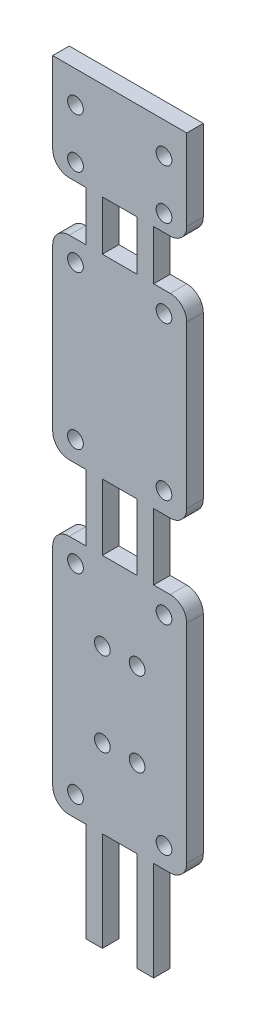
SolidWorks part; units mm, degrees
ref_plane "Front Plane" through (0, 0, 0) normal (0, 0, 1) x (1, 0, 0)
ref_plane "Top Plane" through (0, 0, 0) normal (0, 1, 0) x (1, 0, 0)
ref_plane "Right Plane" through (0, 0, 0) normal (1, 0, 0) x (0, 0, -1)
sketch "Sketch1" plane through (0, 0, 0) normal (0, 0, 1) x (1, 0, 0)
  line L0 (4, 26) -> (2, 26)
  line L1 (0, 1.5) -> (16.2, 1.5) construction
  line L2 (0, 14) -> (4, 14) construction
  line L3 (0, 14) -> (0, 1.5) construction
  line L4 (6, 14) -> (6, 26)
  line L5 (4, 14) -> (4, 26)
  line L6 (0, 28) -> (0, 53.14)
  line L7 (0, 94.665) -> (0, 104.46)
  line L8 (6, 14) -> (10.2, 14) construction
  line L9 (8.1, 1.5) -> (8.1, 104.46) construction
  line L10 (0, 104.46) -> (16.2, 104.46)
  line L11 (6, 63.14) -> (10.2, 63.14)
  line L12 (6, 55.14) -> (10.2, 55.14)
  line L13 (6, 92.665) -> (10.2, 92.665)
  line L14 (6, 86.665) -> (10.2, 86.665)
  line L15 (16.2, 84.665) -> (16.2, 65.14)
  line L16 (10.2, 86.665) -> (10.2, 92.665)
  line L17 (14.2, 55.14) -> (12.2, 55.14)
  line L18 (2, 92.665) -> (4, 92.665)
  line L19 (2, 86.665) -> (4, 86.665)
  line L20 (2, 63.14) -> (4, 63.14)
  line L21 (10.2, 55.14) -> (10.2, 63.14)
  line L22 (4, 86.665) -> (4, 92.665)
  line L23 (4, 55.14) -> (4, 63.14)
  line L24 (6, 55.14) -> (6, 63.14)
  line L25 (2, 55.14) -> (4, 55.14)
  line L26 (6, 86.665) -> (6, 92.665)
  line L27 (12.2, 55.14) -> (12.2, 63.14)
  line L28 (12.2, 86.665) -> (12.2, 92.665)
  line L29 (14.2, 63.14) -> (12.2, 63.14)
  line L30 (14.2, 86.665) -> (12.2, 86.665)
  line L31 (14.2, 92.665) -> (12.2, 92.665)
  line L32 (6, 26) -> (10.2, 26)
  line L33 (4, 14) -> (6, 14)
  line L34 (16.2, 94.665) -> (16.2, 104.46)
  line L35 (16.2, 28) -> (16.2, 53.14)
  line L36 (12.2, 14) -> (12.2, 26)
  line L37 (10.2, 14) -> (10.2, 26)
  line L38 (16.2, 14) -> (16.2, 1.5) construction
  line L39 (16.2, 14) -> (12.2, 14) construction
  line L40 (12.2, 26) -> (14.2, 26)
  line L41 (10.2, 14) -> (12.2, 14)
  line L58 (0, 84.665) -> (0, 65.14)
  circle A0 centre (2.85, 11.5) radius 0.95 construction
  circle A1 centre (13.45, 94.665) radius 0.95
  circle A2 centre (13.45, 84.165) radius 0.95
  circle A3 centre (2.85, 5.5) radius 0.95 construction
  circle A4 centre (13.45, 65.64) radius 0.95
  circle A5 centre (13.45, 52.64) radius 0.95
  circle A6 centre (13.45, 28.5) radius 0.95
  circle A7 centre (10.2, 35.5) radius 0.95
  arc A8 (16.2, 28) -> (14.2, 26) centre (14.2, 28) cw
  circle A9 centre (10.2, 45.64) radius 0.95
  arc A10 (2, 86.665) -> (0, 84.665) centre (2, 84.665) ccw
  arc A11 (14.2, 55.14) -> (16.2, 53.14) centre (14.2, 53.14) cw
  circle A12 centre (13.45, 100.665) radius 0.95
  arc A13 (16.2, 94.665) -> (14.2, 92.665) centre (14.2, 94.665) cw
  arc A14 (16.2, 65.14) -> (14.2, 63.14) centre (14.2, 65.14) cw
  arc A15 (0, 65.14) -> (2, 63.14) centre (2, 65.14) ccw
  arc A16 (0, 94.665) -> (2, 92.665) centre (2, 94.665) ccw
  arc A17 (14.2, 86.665) -> (16.2, 84.665) centre (14.2, 84.665) cw
  circle A18 centre (2.75, 100.665) radius 0.95
  circle A19 centre (13.35, 5.5) radius 0.95 construction
  circle A20 centre (13.35, 11.5) radius 0.95 construction
  arc A22 (2, 55.14) -> (0, 53.14) centre (2, 53.14) ccw
  circle A24 centre (6, 45.64) radius 0.95
  arc A26 (0, 28) -> (2, 26) centre (2, 28) ccw
  circle A30 centre (6, 35.5) radius 0.95
  circle A32 centre (2.75, 28.5) radius 0.95
  circle A34 centre (2.75, 52.64) radius 0.95
  circle A36 centre (2.75, 65.64) radius 0.95
  circle A38 centre (2.75, 84.165) radius 0.95
  circle A40 centre (2.75, 94.665) radius 0.95
  point P9 (8.1, 92.665)
  point P11 (8.1, 86.665)
  point P16 (8.1, 63.14)
  point P17 (8.1, 55.14)
  point P20 (8.1, 63.14)
  point P21 (8.1, 55.14)
  point P58 (8.1, 26)
  point P66 (8.1, 14)
  point P83 (8.1, 26)
  point P96 (8.1, 92.665)
  point P100 (8.1, 14)
  dimension "D11" = 2.75
  dimension "D12" = 6
  dimension "D13" = 2.5
  dimension "D14" = 9.5
  dimension "D15" = 2.75
  dimension "D16" = 6
  dimension "D8" = 2
  dimension "D28" = 2
  dimension "D30" = 2
  dimension "D32" = 2
  dimension "D42" = 1.9
  dimension "D44" = 2
  dimension "D2" = 2.85
  dimension "D3" = 4
  dimension "D4" = 2.85
  dimension "D5" = 6
  dimension "D6" = 2.5
  dimension "D7" = 12
  dimension "D9" = 2.5
  dimension "D10" = 9.5
  dimension "D17" = 29.14
  dimension "D18" = 2.75
  dimension "D19" = 2.5
  dimension "D20" = 8
  dimension "D21" = 2
  dimension "D22" = 2
  dimension "D23" = 2
  dimension "D24" = 2
  dimension "D25" = 2.75
  dimension "D26" = 2.5
  dimension "D27" = 23.525
  dimension "D39" = 2
  dimension "D40" = 2.75
  dimension "D41" = 6
  dimension "D45" = 2.75
  dimension "D46" = 6
  dimension "D47" = 11.795
  dimension "D48" = 8.1
  dimension "D49" = 2
extrude "Boss-Extrude1" add sketch "Sketch1" along normal blind 2
sketch "Sketch2" plane through (0, 0, 2) normal (0, 0, 1) x (1, 0, 0)
  line L0 (4, 92.665) -> (12.2, 92.665)
  line L1 (12.2, 92.665) -> (12.2, 86.665)
  line L2 (12.2, 86.665) -> (4, 86.665)
  line L3 (4, 86.665) -> (4, 92.665)
  line L4 (4, 63.14) -> (12.2, 63.14)
  line L5 (12.2, 63.14) -> (12.2, 55.14)
  line L6 (12.2, 55.14) -> (4, 55.14)
  line L7 (4, 55.14) -> (4, 63.14)
  line L8 (4, 26) -> (12.2, 26)
  line L9 (12.2, 26) -> (12.2, 14)
  line L10 (12.2, 14) -> (4, 14)
  line L11 (4, 14) -> (4, 26)
extrude "Cut-Extrude1" [suppressed] cut sketch "Sketch2" against normal up to surface (2 mm away)
equation "\"D48@Sketch1\"= ( \"fingerWidth@parametersSketch@prostheticParameters.SLDPRT\" ) / 2 'Ring Width"
equation "\"D17@Sketch1\"= \"HL@parametersSketch@prostheticParameters.SLDPRT\" * 0.244 - 4 - 12'Ring PIP Length"
equation "\"D27@Sketch1\"= \"HL@parametersSketch@prostheticParameters.SLDPRT\" * 0.165 - 3 - 4'Ring MIP Length"
equation "\"D47@Sketch1\"= \"HL@parametersSketch@prostheticParameters.SLDPRT\" * 0.107 - 3 - 5'Ring DIP Length - Gap fingertip"
equation "\"D42@Sketch1\"= 1.5 + \"tol1@parametersSketch@prostheticParameters.SLDPRT\""
